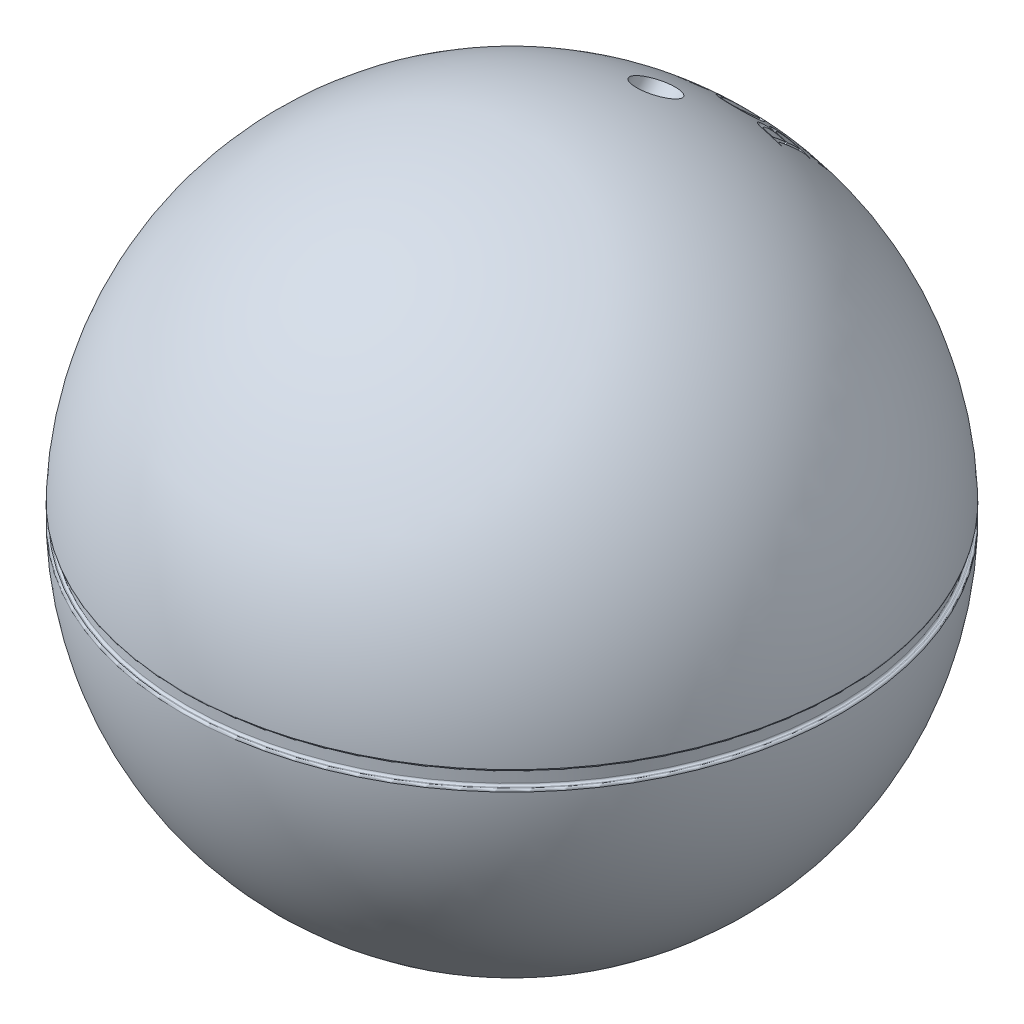
SolidWorks part; units mm, degrees
ref_plane "Front Plane" through (0, 0, 0) normal (0, 0, 1) x (1, 0, 0)
ref_plane "Top Plane" through (0, 0, 0) normal (0, 1, 0) x (1, 0, 0)
ref_plane "Right Plane" through (0, 0, 0) normal (1, 0, 0) x (0, 0, -1)
sketch "Sketch1" plane through (0, 0, 0) normal (0, 0, 1) x (1, 0, 0)
  line L0 (0, 54.5337) -> (0, -75.8802) construction
  line L1 (0, -27.5) -> (17.2627, -27.5)
  line L2 (0, 32.5) -> (0, -27.5)
  line L3 (-36.8745, 0) -> (36.0037, 0) construction
  line L5 (32.2, 0.75) -> (32.286, 0.75)
  line L6 (32, 0.55) -> (32, -0.55)
  line L7 (32.2, -0.75) -> (32.286, -0.75)
  line L9 (32, 0.75) -> (33, -0.75) construction
  line L10 (32, -0.75) -> (33, 0.75) construction
  arc A0 (17.3696, -27.469) -> (32.4859, -0.9559) centre (0, 0) ccw
  arc A1 (32.4859, 0.9559) -> (0, 32.5) centre (0, 0) ccw
  arc A2 (32.286, -0.75) -> (32.4859, -0.9559) centre (32.286, -0.95) cw
  arc A3 (32.2, -0.75) -> (32, -0.55) centre (32.2, -0.55) cw
  arc A4 (32, 0.55) -> (32.2, 0.75) centre (32.2, 0.55) cw
  arc A5 (32.286, 0.75) -> (32.4859, 0.9559) centre (32.286, 0.95) ccw
  arc A6 (17.2627, -27.5) -> (17.3696, -27.469) centre (17.2627, -27.3) ccw
  point P11 (32.5, 0)
  point P27 (32.4913, 0.75)
  dimension "D1" = 65
  dimension "D5" = 0.2
  dimension "D6" = 0.2
  dimension "D2" = 60
  dimension "D3" = 1.5
  dimension "D4" = 32
revolve "Revolve1" add sketch "Sketch1" angle 360 about L0
ref_plane "Plane1" through (0, 0, 0) normal (0, -0.7071, 0.7071) x (1, 0, 0)
ref_plane "Plane2" through (0, 35.3553, -35.3553) normal (0, -0.7071, 0.7071) x (1, 0, 0)
sketch "Sketch2" plane through (0, 35.3553, -35.3553) normal (0, -0.7071, 0.7071) x (1, 0, 0)
  line L0 (-25.1198, 0) -> (28.9748, 0) construction
  line L1 (7, -2.6125) -> (-7, -2.6125) construction
  line L2 (8.1158, 6.3962) -> (8.1158, -5.6475) construction
  line L3 (0, 7.4256) -> (0, -7.8778) construction
  circle A0 centre (0, 10.5824) radius 2
  text T0 "   BOSS" font "Times New Roman" height in points 16
  text T1 "HUGO BOSS" font "Arial" height in points 5
  dimension "D1" = 14
extrude "Cut-Extrude2" cut sketch "Sketch2" along normal blind 20.5
